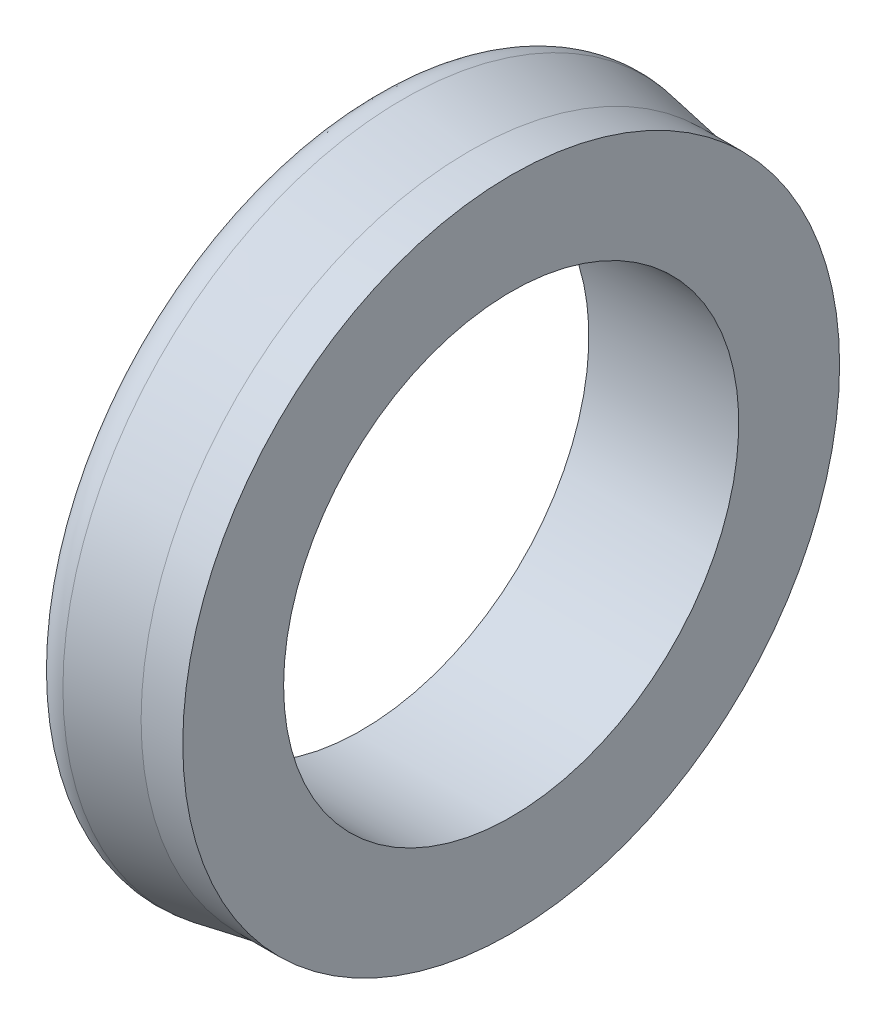
SolidWorks part; units mm, degrees
ref_plane "Face" through (0, 0, 0) normal (0, 0, 1) x (1, 0, 0)
ref_plane "Dessus" through (0, 0, 0) normal (0, 1, 0) x (1, 0, 0)
ref_plane "Droite" through (0, 0, 0) normal (1, 0, 0) x (0, 0, -1)
sketch "Esquisse1" plane through (0, 0, 0) normal (0, 0, 1) x (1, 0, 0)
  line L0 (-5, 0) -> (11, 0) construction
  line L1 (0, 8.35) -> (5.5, 8.35)
  line L2 (5.5, 8.35) -> (5.5, 12.05)
  line L3 (5.5, 12.05) -> (3.9713, 12.05)
  line L4 (3.9713, 12.05) -> (1.5366, 12.4845)
  line L5 (0, 8.35) -> (0, 10.15)
  line L6 (0, 10.15) -> (2.7, 10.15)
  line L7 (2.7703, 10.9438) -> (0.5, 11.3489)
  line L8 (0.6, 12.1489) -> (0.5, 11.3489)
  arc A0 (2.7, 10.15) -> (2.7703, 10.9438) centre (2.7, 10.55) ccw
  arc A1 (1.5366, 12.4845) -> (0.6, 12.1489) centre (1.3609, 11.5) ccw
  dimension "D5" = 1
  dimension "D6" = 0.4
  dimension "D10" = 2.7
  dimension "D8" = 12.5
  dimension "D1" = 8.35
  dimension "D2" = 1.8
  dimension "D3" = 3.7
  dimension "D4" = 1.3
  dimension "D7" = 0.8
  dimension "D9" = 5.5
  dimension "D11" = 0.5
  dimension "D12" = 0.6
revolve "Base-Révolution" add sketch "Esquisse1" angle 360 about L0
